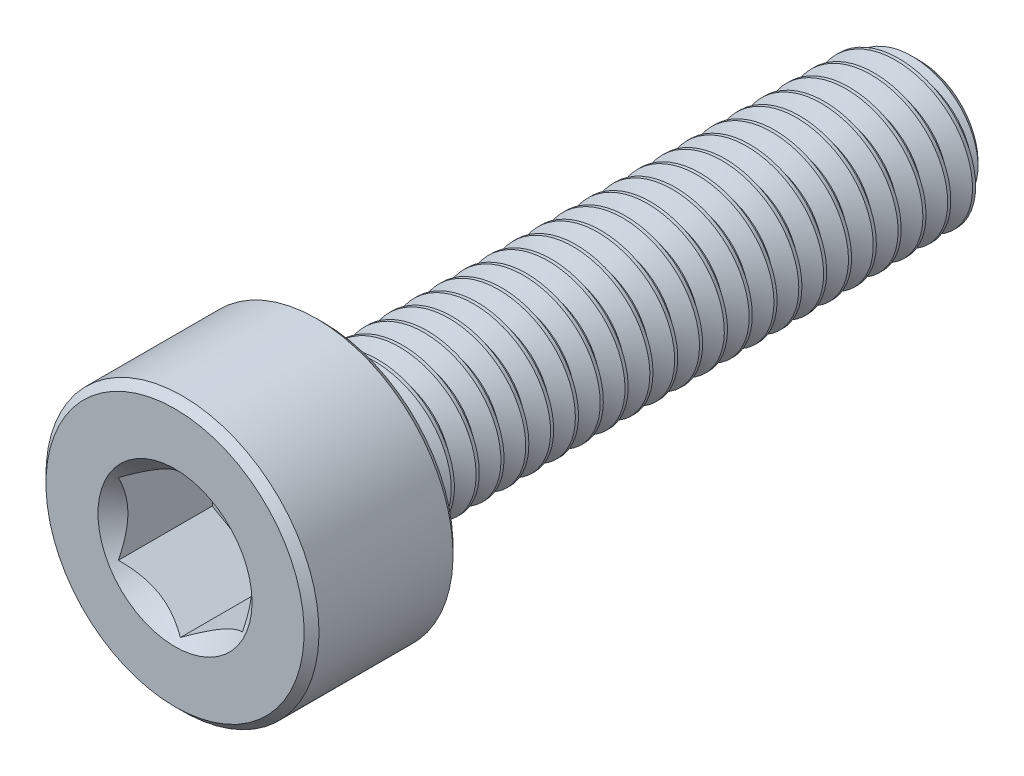
SolidWorks part; units mm, degrees
ref_plane "Front Plane" through (0, 0, 0) normal (0, 0, 1) x (1, 0, 0)
ref_plane "Top Plane" through (0, 0, 0) normal (0, 1, 0) x (1, 0, 0)
ref_plane "Right Plane" through (0, 0, 0) normal (1, 0, 0) x (0, 0, -1)
sketch "Sketch1" plane through (0, 0, 0) normal (1, 0, 0) x (0, 0, -1)
  line L0 (-7.5, 0) -> (7.5, 0) construction
  line L1 (7.5, 0) -> (7.5, 1.1752) construction
  line L2 (7.5, 1.1752) -> (7.1752, 1.5) construction
  line L3 (7.1752, 1.5) -> (7.125, 1.5) construction
  line L4 (7.125, 1.5) -> (-4.5, 1.5) construction
  line L5 (-4.5, 1.5) -> (-4.5, 2.75) construction
  line L6 (-4.5, 2.75) -> (-7.5, 2.75) construction
  line L7 (-7.5, 2.75) -> (-7.5, 0) construction
  line L8 (7.5, 1.1752) -> (7.5, 1.5) construction
  line L9 (7.4687, 1.5541) -> (7.7187, 1.1211) construction
  line L10 (7.7187, 1.1211) -> (7.9687, 1.5541) construction
  line L11 (7.9687, 1.5541) -> (7.4687, 1.5541) construction
  line L12 (7.7187, 1.5541) -> (7.7188, 1.5) construction
  line L13 (7.7187, 1.1211) -> (7.7187, 1.1752) construction
  line L14 (7.6875, 1.1752) -> (7.75, 1.1752) construction
  line L15 (7.5, 1.5) -> (7.9375, 1.5) construction
  line L16 (7.4844, 1.5271) -> (7.9531, 1.5271) construction
  line L17 (7.5, 0) -> (7.5, -1.5) construction
  line L18 (-4.65, 2.75) -> (-4.5, 2.6) construction
  line L19 (-7.35, 2.75) -> (-7.5, 2.6) construction
  line L20 (-4.5, 1.5) -> (-4.5, 0) construction
  line L21 (-4.5, 0.75) -> (-0.5, 0.75) construction
  line L22 (-0.5, 0.75) -> (3.5, 0.75) construction
  line L23 (3.5, 0.75) -> (7.5, 0.75) construction
  line L24 (-0.5, 0.75) -> (-0.5, 1.5) construction
  line L25 (-0.5, 1.5) -> (-0.5, 2.75) construction
  line L26 (3.5, 0.75) -> (3.5, 2.75) construction
  point P0 (-7.5, 1.25)
  point P3 (6.25, 1.5)
  point P4 (0, 0)
  point P18 (3.5, 1.5)
  point P22 (7.7187, 1.1752)
  point P24 (7.125, 1.5)
  point P25 (7.7188, 1.5)
  point P28 (7.7187, 1.5271)
  point P29 (6.25, -1.5)
  point P30 (-0.5, 1.5)
  point P31 (-6, 2.75)
  point P37 (-5.025, 2.75)
  point P38 (-7.275, 2.75)
  point P45 (-0.5, 0.75)
  point P46 (3.5, 0.75)
  dimension "D2" = 0.0625
  dimension "D7" = 0.15
  dimension "D8" = 0.15
  dimension "D9" = 0.15
  dimension "D10" = 0.075
  dimension "D11" = 0.375
  dimension "Drive Size" = 2.5
  dimension "Head Diameter" = 5.5
  dimension "Head Height" = 3
  dimension "Thread Pitch" = 0.5
  dimension "Thread Dia" = 3
  dimension "Length" = 12
  dimension "D12" = 0.375
  dimension "D4" = 1.25
  dimension "D3" = 45
sketch "Sketch2" plane through (0, 0, 0) normal (1, 0, 0) x (0, 0, -1)
  line L0 (-7.5, 0) -> (-7.5, 2.6)
  line L1 (-7.35, 2.75) -> (-4.65, 2.75)
  line L2 (-4.5, 2.6) -> (-4.5, 1.65)
  line L4 (7.1752, 1.5) -> (7.5, 1.1752)
  line L5 (7.5, 1.1752) -> (7.5, 0)
  line L6 (-4.5, 2.75) -> (-7.5, 2.75) construction
  line L7 (7.5, 0) -> (-7.5, 0)
  line L8 (-7.35, 2.75) -> (-7.5, 2.6) construction
  line L10 (-7.35, 2.75) -> (-7.5, 2.6)
  line L14 (-4.65, 2.75) -> (-4.5, 2.6) construction
  line L16 (-4.65, 2.75) -> (-4.5, 2.6)
  line L17 (-4.5, 1.5) -> (-4.5, 2.75) construction
  line L19 (-4.35, 1.5) -> (7.1752, 1.5)
  line L20 (7.125, 1.5) -> (-4.5, 1.5) construction
  arc A1 (-4.5, 1.65) -> (-4.35, 1.5) centre (-4.35, 1.65) ccw
  dimension "D3" = 0.15
revolve "Revolve1" add sketch "Sketch2" angle 360 about L7
sketch "Sketch3" plane through (0, 0, 7.5) normal (0, 0, 1) x (1, 0, 0)
  line L1 (1.25, -0.7217) -> (1.25, 0.7217)
  line L2 (1.25, 0.7217) -> (0, 1.4434)
  line L3 (0, 1.4434) -> (-1.25, 0.7217)
  line L4 (-1.25, 0.7217) -> (-1.25, -0.7217)
  line L5 (-1.25, -0.7217) -> (0, -1.4434)
  line L6 (0, -1.4434) -> (1.25, -0.7217)
  circle A0 centre (0, 0) radius 1.25 construction
  circle A1 centre (0, 0) radius 2.75 construction
  circle A2 centre (0, 0) radius 2.75 construction
  circle A3 centre (0, 0) radius 1.4434 construction
  point P13 (0, 0)
  dimension "D1" = 2.8868
extrude "Cut-Extrude1" cut sketch "Sketch3" against normal offset from surface (2 mm away) 1 up to face at (0, 2.6, 4.5)
sketch "Sketch4" plane through (0, 0, 7.5) normal (0, 0, 1) x (1, 0, 0)
  circle A0 centre (0, 0) radius 1.5516
  dimension "D1" = 3.1033
extrude "Cut-Extrude2" cut sketch "Sketch4" against normal up to vertex (1.5 mm away) draft 45 up to point (0, 2.75, 6)
sketch "Sketch11" plane through (0, 0, 0) normal (1, 0, 0) x (0, 0, -1)
  line L0 (-7.5, 0) -> (7.5, 0) construction
  line L1 (-7.5, 0) -> (7.5, 0) construction
  line L2 (-2.25, 0) -> (-2.25, 1.5) construction
  line L3 (7.125, 1.5) -> (-4.5, 1.5) construction
  line L4 (5.25, 0) -> (5.25, 1.5) construction
  line L6 (7.5, 1.1752) -> (7.5, 1.5) construction
  point P2 (-2.25, 0)
  point P3 (5.25, 0)
  dimension "D1" = 2.25
  dimension "D2" = 2.25
sketch "Sketch6" plane through (0, 0, -7.5) normal (0, 0, -1) x (-1, 0, 0)
  circle A0 centre (0, 0) radius 1.5
curve "Helix/Spiral1" pitch 0.5 height 12.5 turns 25
sketch "Sketch10" plane through (0, 0, 0) normal (1, 0, 0) x (0, 0, -1)
  line L0 (-4.35, -2.75) -> (-4.35, 2.75)
  line L5 (-7.5, 0) -> (7.5, 0) construction
  line L6 (-4.35, 1.5) -> (-4.35, -1.5) construction
  point P3 (-4.35, 0)
split "Split1" trim tools "Sketch10" bodies to split 106 resulting bodies 114 115
sketch "Sketch7" plane through (0, 0, 0) normal (1, 0, 0) x (0, 0, -1)
  line L0 (7.4844, 1.5271) -> (7.9531, 1.5271)
  line L1 (7.9531, 1.5271) -> (7.75, 1.1752)
  line L2 (7.75, 1.1752) -> (7.6875, 1.1752)
  line L3 (7.6875, 1.1752) -> (7.4844, 1.5271)
sweep "Cut-Sweep1" cut profiles "Sketch7" path "Helix/Spiral1"
sketch "Sketch8" plane through (0, 0, 0) normal (1, 0, 0) x (0, 0, -1)
  line L0 (-4.5, 0) -> (-4.5, 1.5)
  line L1 (-4.35, -1.5) -> (-4.35, 1.5) construction
  line L2 (-4.5, 1.5) -> (-4.35, 1.5)
  line L4 (-4.35, 1.5) -> (-3.484, 0)
  line L5 (-3.484, 0) -> (-4.5, 0)
  line L6 (7.125, 1.5) -> (-4.5, 1.5) construction
  line L7 (-7.5, 0) -> (7.5, 0) construction
  dimension "D1" = 60
revolve "Revolve2" add sketch "Sketch8" angle 360 about L5
equation "\"D2@Sketch1\" = \"Thread Pitch@Sketch1\" / 8"
equation "\"D4@Helix/Spiral1\" = \"Thread Pitch@Sketch1\""
equation "\"D7@Sketch1\" = \"Head Height@Sketch1\" * .05"
equation "\"D8@Sketch1\"=\"D7@Sketch1\""
equation "\"D9@Sketch1\"=\"D7@Sketch1\""
equation "\"D10@Sketch1\"=\"D7@Sketch1\"/2"
equation "\"D11@Sketch1\"=\"D10@Sketch1\"*5"
equation "\"D4@Sketch1\"=\"Thread Pitch@Sketch1\"*2.5"
equation "\"D12@Sketch1\"=\"Thread Pitch@Sketch1\"*.75"
equation "\"D3@Helix/Spiral1\"=\"Length@Sketch1\"+\"Thread Pitch@Sketch1\""
equation "\"D3@Sketch2\"=\"Thread Dia@Sketch1\"*0.05"
equation "\"D1@Sketch11\"=\"Length@Sketch1\"*0.1875"
equation "\"D2@Sketch11\"=\"D1@Sketch11\""
equation "\"D1@Sketch4\"=\"D1@Sketch3\"*1.075"
